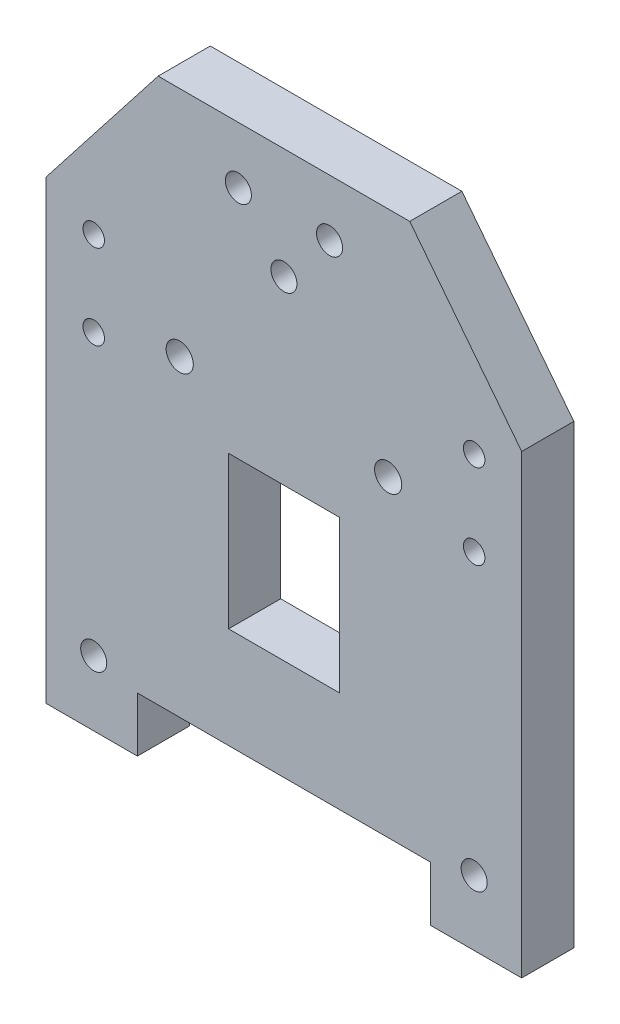
SolidWorks part; units mm, degrees
ref_plane "Plano frontal" through (0, 0, 0) normal (0, 0, 1) x (1, 0, 0)
ref_plane "Plano superior" through (0, 0, 0) normal (0, 1, 0) x (1, 0, 0)
ref_plane "Plano direito" through (0, 0, 0) normal (1, 0, 0) x (0, 0, -1)
sketch "Esboço1" plane through (0, 0, 0) normal (0, 0, 1) x (1, 0, 0)
  line L0 (0, 47.2571) -> (8.5, 47.2571)
  line L1 (0, 47.2571) -> (-8.5, 47.2571)
  line L2 (0, 23.9177) -> (8.5, 23.9177)
  line L3 (0, 23.9177) -> (-8.5, 23.9177)
  line L4 (0, 8.4) -> (0, 75) construction
  line L5 (0, 56.3545) -> (-16, 56.3545) construction
  line L6 (0, 56.3545) -> (16, 56.3545) construction
  line L7 (8.5, 47.2571) -> (8.5, 23.9177)
  line L8 (-8.5, 47.2571) -> (-8.5, 23.9177)
  line L20 (19.3117, 92) -> (-19.3117, 92)
  line L21 (-19.3117, 92) -> (-36.5, 70)
  line L22 (-36.5, 70) -> (-36.5, 0)
  line L23 (-36.5, 0) -> (-22.5, 0)
  line L24 (-22.5, 0) -> (-22.5, 8.4)
  line L25 (-22.5, 8.4) -> (22.5, 8.4)
  line L26 (22.5, 8.4) -> (22.5, 0)
  line L27 (22.5, 0) -> (36.5, 0)
  line L28 (36.5, 0) -> (36.5, 70)
  line L29 (36.5, 70) -> (19.3117, 92)
  circle A13 centre (0, 75) radius 2
  circle A14 centre (-7, 83.3) radius 2
  circle A15 centre (7, 83.3) radius 2
  circle A20 centre (-29.2, 10) radius 2
  circle A21 centre (29.2, 10) radius 2
  circle A26 centre (-16, 56.3545) radius 2.0867
  circle A27 centre (16, 56.3545) radius 2.0867
  point P31 (0, 23.9177)
  point P33 (0, 47.2571)
extrude "Ressalto-extrusão1" add sketch "Esboço1" along normal blind 8
sketch "Esboço3" plane through (0, 0, 8) normal (0, 0, 1) x (1, 0, 0)
  line L0 (-36.5, 70) -> (-36.5, 92) construction
  line L1 (-36.5, 92) -> (-29.2, 92) construction
  line L2 (-19.3117, 92) -> (-36.5, 92) construction
  line L3 (-29.2, 92) -> (-29.2, 66) construction
  circle A0 centre (-29.2, 66) radius 1.3438 construction
sketch "Esboço4" plane through (0, 0, 8) normal (0, 0, 1) x (1, 0, 0)
  line L1 (-29.2, 66) -> (29.2, 66) construction
  line L2 (-29.2, 66) -> (-29.2, 53) construction
  line L3 (-29.2, 53) -> (29.2, 53) construction
  line L4 (29.2, 66) -> (29.2, 53) construction
  circle A0 centre (-29.2, 66) radius 1.65
  circle A1 centre (-29.2, 53) radius 1.65
  circle A2 centre (29.2, 53) radius 1.65
  circle A3 centre (29.2, 66) radius 1.65
extrude "Corte-extrusão1" cut sketch "Esboço4" against normal through all
